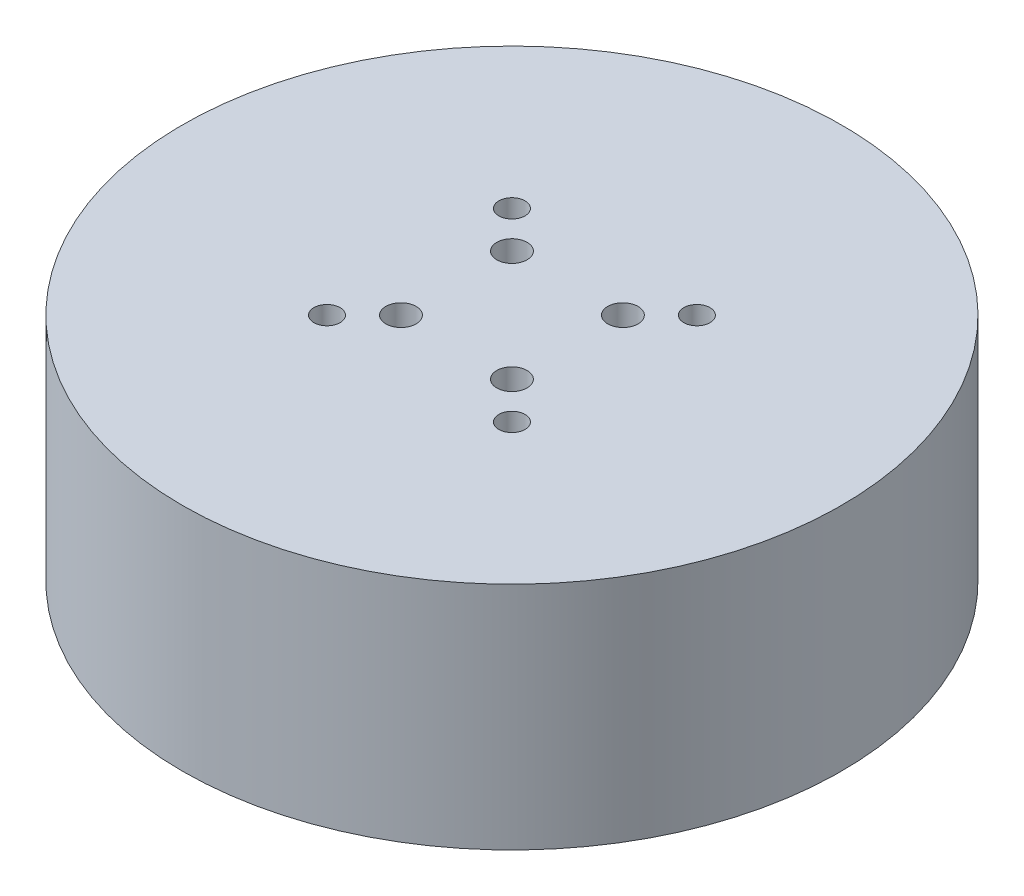
SolidWorks part; units mm, degrees
ref_plane "Front Plane" through (0, 0, 0) normal (0, 0, 1) x (1, 0, 0)
ref_plane "Top Plane" through (0, 0, 0) normal (0, 1, 0) x (1, 0, 0)
ref_plane "Right Plane" through (0, 0, 0) normal (1, 0, 0) x (0, 0, -1)
sketch "Sketch1" plane through (0, 0, 0) normal (0, 1, 0) x (1, 0, 0)
  circle A0 centre (0, 0) radius 31.5
extrude "Boss-Extrude1" add sketch "Sketch1" along normal blind 22
hole_wizard "Tap Drill for M3x0.5 Tap1" positions "Sketch6" profile "Sketch5" hole size "M3x0.5" standard "ANSI Metric"
sketch "Sketch6" plane through (0, 22, 0) normal (0, 1, 0) x (1, 0, 0)
  line L0 (0, 0) -> (8.8388, 8.8388) construction
  line L2 (0, 0) -> (8.8388, -8.8388) construction
  line L4 (0, 0) -> (-8.8388, -8.8388) construction
  line L6 (0, 0) -> (-8.8388, 8.8388) construction
  point P2 (8.8388, 8.8388)
  point P7 (8.8388, -8.8388)
  point P12 (-8.8388, -8.8388)
  point P16 (-8.8388, 8.8388)
sketch "Sketch5" plane through (8.8388, 22, -8.8388) normal (1, 0, 0) x (0, 0, 1)
  line L0 (0, 0) -> (0, 5.5111)
  line L1 (0, 5.5111) -> (1.25, 4.76)
  line L2 (1.25, 4.76) -> (1.25, 0)
  line L5 (1.25, 0) -> (0, 0)
  line L10 (0, 5.5111) -> (-1.25, 4.76) construction
  line L11 (0, -6.35) -> (0, 107.95) construction
  dimension "Hole Dia." = 2.5
  dimension "Hole Depth" = 4.76
  dimension "Drill Angle" = 118
hole_wizard "Tap Drill for M2.5x0.45 Tap1" positions "Sketch8" profile "Sketch7" hole size "M2.5x0.45" standard "ANSI Metric"
sketch "Sketch8" plane through (0, 0, 0) normal (0, -1, 0) x (-1, 0, 0)
  line L2 (0, 0) -> (5.3033, -5.3033) construction
  line L4 (0, 0) -> (5.3033, 5.3033) construction
  line L6 (0, 0) -> (-5.3033, -5.3033) construction
  line L8 (0, 0) -> (-5.3033, 5.3033) construction
  point P7 (5.3033, -5.3033)
  point P13 (5.3033, 5.3033)
  point P17 (-5.3033, -5.3033)
  point P22 (-5.3033, 5.3033)
sketch "Sketch7" plane through (-5.3033, 0, 5.3033) normal (1, 0, 0) x (0, 0, -1)
  line L0 (0, 0) -> (0, 4.1159)
  line L1 (0, 4.1159) -> (1.025, 3.5)
  line L2 (1.025, 3.5) -> (1.025, 0)
  line L5 (1.025, 0) -> (0, 0)
  line L10 (0, 4.1159) -> (-1.025, 3.5) construction
  line L11 (0, -6.35) -> (0, 107.95) construction
  dimension "Hole Dia." = 2.05
  dimension "Hole Depth" = 3.5
  dimension "Drill Angle" = 118
hole_wizard "M2.5 Clearance Hole1" positions "Sketch10" profile "Sketch9" hole size "M2.5" standard "ANSI Metric" end condition through all
sketch "Sketch10" plane through (0, 22, 0) normal (0, 1, 0) x (1, 0, 0)
  line L0 (0, 0) -> (5.3033, 5.3033) construction
  line L2 (0, 0) -> (5.3033, -5.3033) construction
  line L4 (0, 0) -> (-5.3033, -5.3033) construction
  line L5 (-5.3033, -5.3033) -> (0, 0)
  line L8 (0, 0) -> (-5.3033, 5.3033)
  point P2 (5.3033, 5.3033)
  point P9 (5.3033, -5.3033)
  point P13 (-5.3033, -5.3033)
  point P21 (-5.3033, 5.3033)
sketch "Sketch9" plane through (5.3033, 22, -5.3033) normal (1, 0, 0) x (0, 0, 1)
  line L0 (0, 0) -> (0, 22)
  line L1 (0, 22) -> (1.45, 22)
  line L2 (1.45, 22) -> (1.45, 0)
  line L5 (1.45, 0) -> (0, 0)
  line L11 (0, -6.35) -> (0, 107.95) construction
  dimension "Thru Hole Dia." = 2.9
  dimension "Thru Hole Depth" = 22
